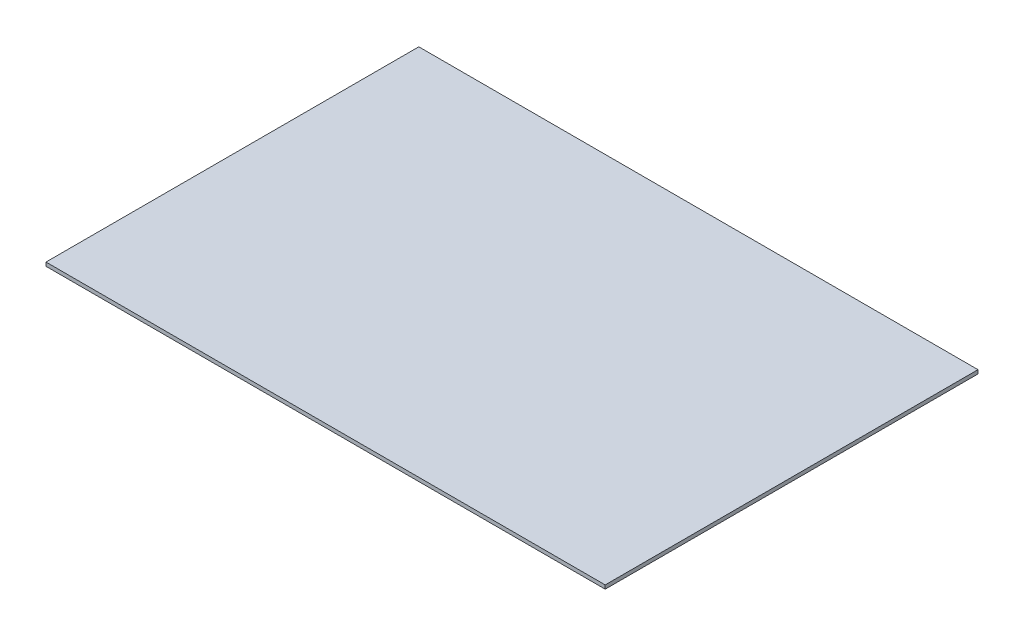
SolidWorks part; units mm, degrees
ref_plane "Face" through (0, 0, 0) normal (0, 0, 1) x (1, 0, 0)
ref_plane "Dessus" through (0, 0, 0) normal (0, 1, 0) x (1, 0, 0)
ref_plane "Droite" through (0, 0, 0) normal (1, 0, 0) x (0, 0, -1)
sketch "Esquisse1" plane through (0, 0, 0) normal (0, 1, 0) x (1, 0, 0)
  line L1 (0, 0) -> (1500, 0)
  line L2 (0, 0) -> (0, 1000)
  line L3 (0, 1000) -> (1500, 1000)
  line L4 (1500, 0) -> (1500, 1000)
  dimension "D1" = 1000
  dimension "D2" = 1500
extrude "Extrusion1" add sketch "Esquisse1" along normal blind 10
